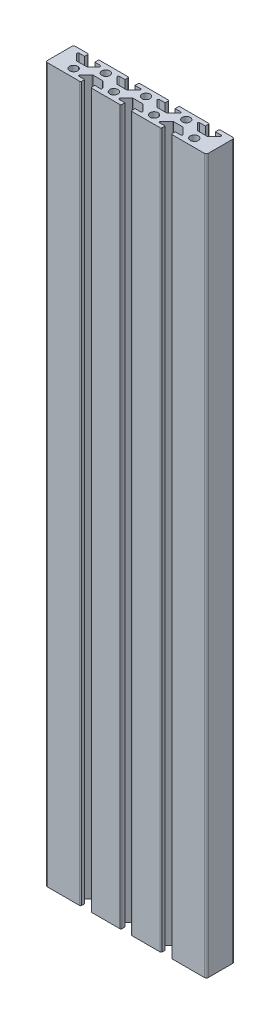
SolidWorks part; units mm, degrees
ref_plane "Front Plane" through (0, 0, 0) normal (0, 0, 1) x (1, 0, 0)
ref_plane "Top Plane" through (0, 0, 0) normal (0, 1, 0) x (1, 0, 0)
ref_plane "Right Plane" through (0, 0, 0) normal (1, 0, 0) x (0, 0, -1)
sketch "Sketch1" plane through (0, 0, 0) normal (0, 1, 0) x (1, 0, 0)
  line L0 (63.5, 12) -> (67.5, 12)
  line L1 (0, 0) -> (80, 0)
  line L2 (0, 0) -> (0, 14)
  line L3 (0, 14) -> (80, 14)
  line L4 (80, 0) -> (80, 14)
  line L5 (67.5, 12) -> (67.5, 14)
  line L6 (67.5, 14) -> (72.5, 14)
  line L7 (72.5, 14) -> (72.5, 12)
  line L9 (76.5, 12) -> (72.5, 8)
  line L10 (72.5, 8) -> (67.5, 8)
  line L11 (67.5, 8) -> (63.5, 12)
  line L12 (72.5, 12) -> (76.5, 12)
  line L13 (52.5, 12) -> (56.5, 12)
  line L14 (56.5, 12) -> (52.5, 8)
  line L15 (52.5, 8) -> (47.5, 8)
  line L16 (47.5, 8) -> (43.5, 12)
  line L17 (43.5, 12) -> (47.5, 12)
  line L18 (47.5, 12) -> (47.5, 14)
  line L19 (47.5, 14) -> (52.5, 14)
  line L20 (52.5, 14) -> (52.5, 12)
  line L21 (32.5, 12) -> (36.5, 12)
  line L22 (36.5, 12) -> (32.5, 8)
  line L23 (32.5, 8) -> (27.5, 8)
  line L24 (27.5, 8) -> (23.5, 12)
  line L25 (23.5, 12) -> (27.5, 12)
  line L26 (27.5, 12) -> (27.5, 14)
  line L27 (27.5, 14) -> (32.5, 14)
  line L28 (32.5, 14) -> (32.5, 12)
  line L29 (12.5, 12) -> (16.5, 12)
  line L30 (16.5, 12) -> (12.5, 8)
  line L31 (12.5, 8) -> (7.5, 8)
  line L32 (7.5, 8) -> (3.5, 12)
  line L33 (3.5, 12) -> (7.5, 12)
  line L34 (7.5, 12) -> (7.5, 14)
  line L35 (7.5, 14) -> (12.5, 14)
  line L36 (12.5, 14) -> (12.5, 12)
  line L37 (57.5, 0) -> (57.5, 2)
  line L38 (57.5, 2) -> (53.5, 2)
  line L39 (53.5, 2) -> (57.5, 6)
  line L40 (57.5, 6) -> (62.5, 6)
  line L41 (62.5, 6) -> (66.5, 2)
  line L42 (66.5, 2) -> (62.5, 2)
  line L43 (62.5, 2) -> (62.5, 0)
  line L44 (62.5, 0) -> (57.5, 0)
  line L45 (42.5, 0) -> (37.5, 0)
  line L46 (37.5, 0) -> (37.5, 2)
  line L47 (37.5, 2) -> (33.5, 2)
  line L48 (33.5, 2) -> (37.5, 6)
  line L49 (37.5, 6) -> (42.5, 6)
  line L50 (42.5, 6) -> (46.5, 2)
  line L51 (46.5, 2) -> (42.5, 2)
  line L52 (42.5, 2) -> (42.5, 0)
  line L53 (22.5, 0) -> (17.5, 0)
  line L54 (17.5, 0) -> (17.5, 2)
  line L55 (17.5, 2) -> (13.5, 2)
  line L56 (13.5, 2) -> (17.5, 6)
  line L57 (17.5, 6) -> (22.5, 6)
  line L58 (22.5, 6) -> (26.5, 2)
  line L59 (26.5, 2) -> (22.5, 2)
  line L60 (22.5, 2) -> (22.5, 0)
  circle A0 centre (60, 10) radius 2
  circle A1 centre (40, 10) radius 2
  circle A2 centre (20, 10) radius 2
  circle A3 centre (70, 4) radius 2
  circle A4 centre (50, 4) radius 2
  circle A5 centre (30, 4) radius 2
  circle A6 centre (10, 4) radius 2
  dimension "D17" = 4
  dimension "D21" = 4
  dimension "D1" = 80
  dimension "D2" = 14
  dimension "D3" = 7.5
  dimension "D4" = 5
  dimension "D5" = 6
  dimension "D6" = 17.5
  dimension "D7" = 2
  dimension "D8" = 4
  dimension "D9" = 5
  dimension "D10" = 5
  dimension "D11" = 4
  dimension "D12" = 4
  dimension "D13" = 2
  dimension "D14" = 2
  dimension "D15" = 6
  dimension "D16" = 3
  dimension "D18" = 20
  dimension "D19" = 4
  dimension "D22" = 10
  dimension "D23" = 4
  dimension "D20" = 3
  dimension "D24" = 4
extrude "Boss-Extrude1" add sketch "Sketch1" along normal blind 355 contours L59 L60 L1 L46 L47 L48 L49 L50 L51 L52 L37 L38 L39 L40 L41 L42 L43 L4 L3 L7 L12 L9 L10 L11 L0 L5 L20 L13 L14 L15 L16 L17 L18 L28 L21 L22 L23 L24 L25 L26 L36 L29 L30 L31 L32 L33
fillet "Fillet1" radius 0.5 24 edges at (67.5, 177.5, -8) (63.5, 177.5, -12) (76.5, 177.5, -12) (72.5, 177.5, -8) (47.5, 177.5, -8) (27.5, 177.5, -8) (52.5, 177.5, -8) (32.5, 177.5, -8) (56.5, 177.5, -12) (36.5, 177.5, -12) (43.5, 177.5, -12) (23.5, 177.5, -12) (12.5, 177.5, -8) (7.5, 177.5, -8) (3.5, 177.5, -12) (16.5, 177.5, -12) (72.5, 177.5, -14) (67.5, 177.5, -14) (52.5, 177.5, -14) (47.5, 177.5, -14) (32.5, 177.5, -14) (27.5, 177.5, -14) (12.5, 177.5, -14) (7.5, 177.5, -14)
fillet "Fillet2" radius 0.5 18 edges at (17.5, 177.5, -6) (26.5, 177.5, -2) (22.5, 177.5, -6) (22.5, 177.5, 0) (17.5, 177.5, 0) (13.5, 177.5, -2) (33.5, 177.5, -2) (37.5, 177.5, -6) (42.5, 177.5, -6) (42.5, 177.5, 0) (46.5, 177.5, -2) (37.5, 177.5, 0) (57.5, 177.5, 0) (62.5, 177.5, 0) (53.5, 177.5, -2) (57.5, 177.5, -6) (66.5, 177.5, -2) (62.5, 177.5, -6)
fillet "Fillet3" radius 1 4 edges at (0, 177.5, -14) (0, 177.5, 0) (80, 177.5, -14) (80, 177.5, 0)
sketch "Sketch2" plane through (0, 0, -14) normal (0, 0, -1) x (-1, 0, 0)
  line L0 (-33, 0) -> (-47, 0) construction
  circle A1 centre (-40, 10) radius 2.5
  dimension "D1" = 10
  dimension "D2" = 5
extrude "Cut-Extrude2" cut sketch "Sketch2" against normal blind 230 contours A1
sketch "Sketch3" plane through (0, 0, -14) normal (0, 0, -1) x (-1, 0, 0)
  circle A0 centre (-40, 10) radius 5.5
  dimension "D1" = 11
extrude "Cut-Extrude3" cut sketch "Sketch3" against normal blind 7 contours A0
sketch "Sketch4" plane through (0, 0, -14) normal (0, 0, -1) x (-1, 0, 0)
  line L0 (-33, 355) -> (-47, 355) construction
  circle A0 centre (-40, 345) radius 2.5
  dimension "D1" = 5
  dimension "D2" = 10
extrude "Cut-Extrude4" cut sketch "Sketch4" against normal blind 7
sketch "Sketch5" plane through (0, 0, -14) normal (0, 0, -1) x (-1, 0, 0)
  circle A0 centre (-40, 345) radius 5.5
  dimension "D1" = 11
extrude "Cut-Extrude5" cut sketch "Sketch5" against normal blind 7
